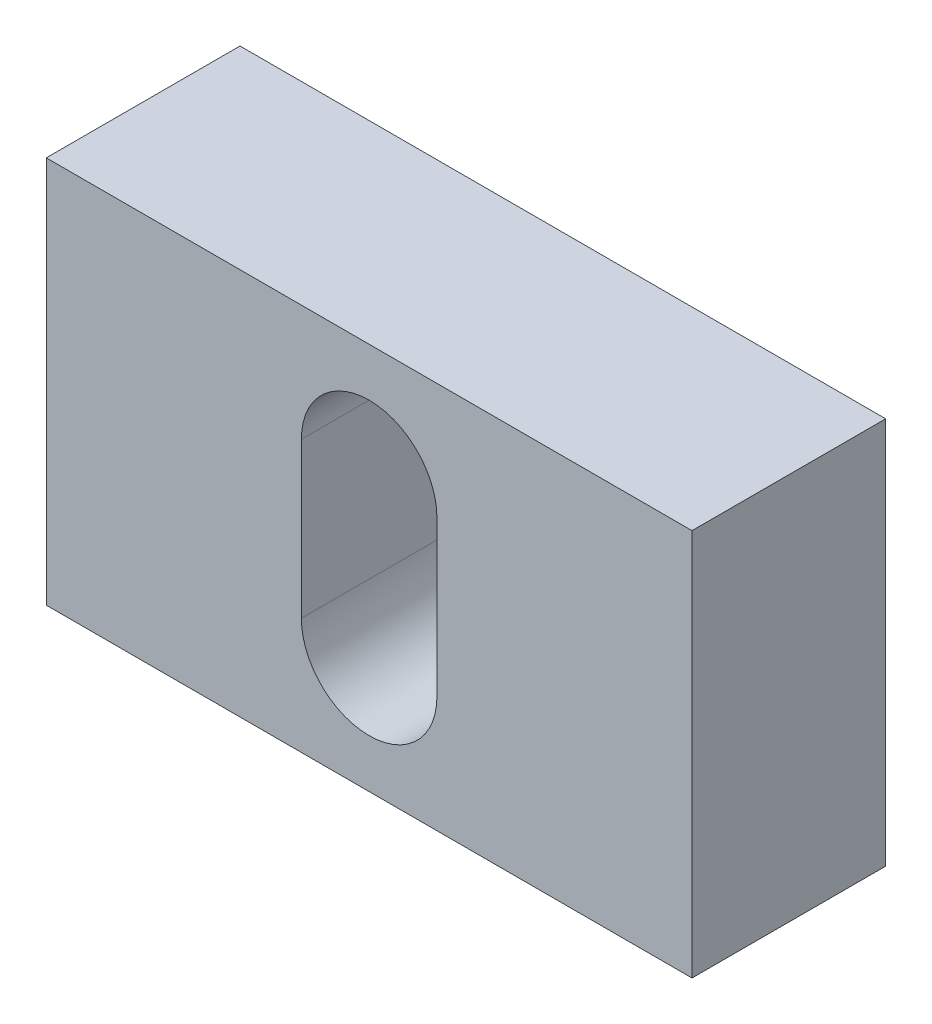
SolidWorks part; units mm, degrees
ref_plane "Plan de face" through (0, 0, 0) normal (0, 0, 1) x (1, 0, 0)
ref_plane "Plan de dessus" through (0, 0, 0) normal (0, 1, 0) x (1, 0, 0)
ref_plane "Plan de droite" through (0, 0, 0) normal (1, 0, 0) x (0, 0, -1)
sketch "Esquisse1" plane through (0, 0, 0) normal (0, 0, 1) x (1, 0, 0)
  line L0 (0, 0) -> (0, 6) construction
  line L1 (-10, 6) -> (10, 6)
  line L2 (-10, 6) -> (-10, -6)
  line L3 (-10, -6) -> (10, -6)
  line L4 (10, 6) -> (10, -6)
  line L5 (0, 0) -> (10, 0) construction
  line L6 (-2.1, 2.4) -> (-2.1, -2.4)
  line L7 (-2.1, -2.4) -> (2.1, -2.4) construction
  line L8 (2.1, -2.4) -> (2.1, 2.4)
  line L9 (2.1, 2.4) -> (-2.1, 2.4) construction
  line L10 (0, 2.4) -> (0, 0) construction
  arc A0 (2.1, 2.4) -> (-2.1, 2.4) centre (0, 2.4) ccw
  arc A1 (-2.1, -2.4) -> (2.1, -2.4) centre (0, -2.4) ccw
  dimension "D3" = 2.1
  dimension "D1" = 12
  dimension "D2" = 20
  dimension "D4" = 4.8
  dimension "D5" = 2.4
extrude "Extrusion1" add sketch "Esquisse1" along normal blind 6
